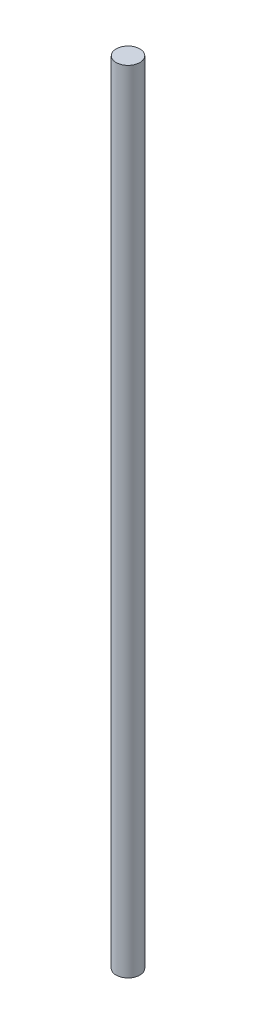
SolidWorks part; units mm, degrees
material "1060 Alloy"
ref_plane "Front Plane" through (0, 0, 0) normal (0, 0, 1) x (1, 0, 0)
ref_plane "Top Plane" through (0, 0, 0) normal (0, 1, 0) x (1, 0, 0)
ref_plane "Right Plane" through (0, 0, 0) normal (1, 0, 0) x (0, 0, -1)
sketch "Sketch1" plane through (0, 0, 0) normal (0, 1, 0) x (1, 0, 0)
  circle A0 centre (0, 0) radius 3
  dimension "D1" = 6
extrude "Boss-Extrude1" add sketch "Sketch1" along normal blind 200
